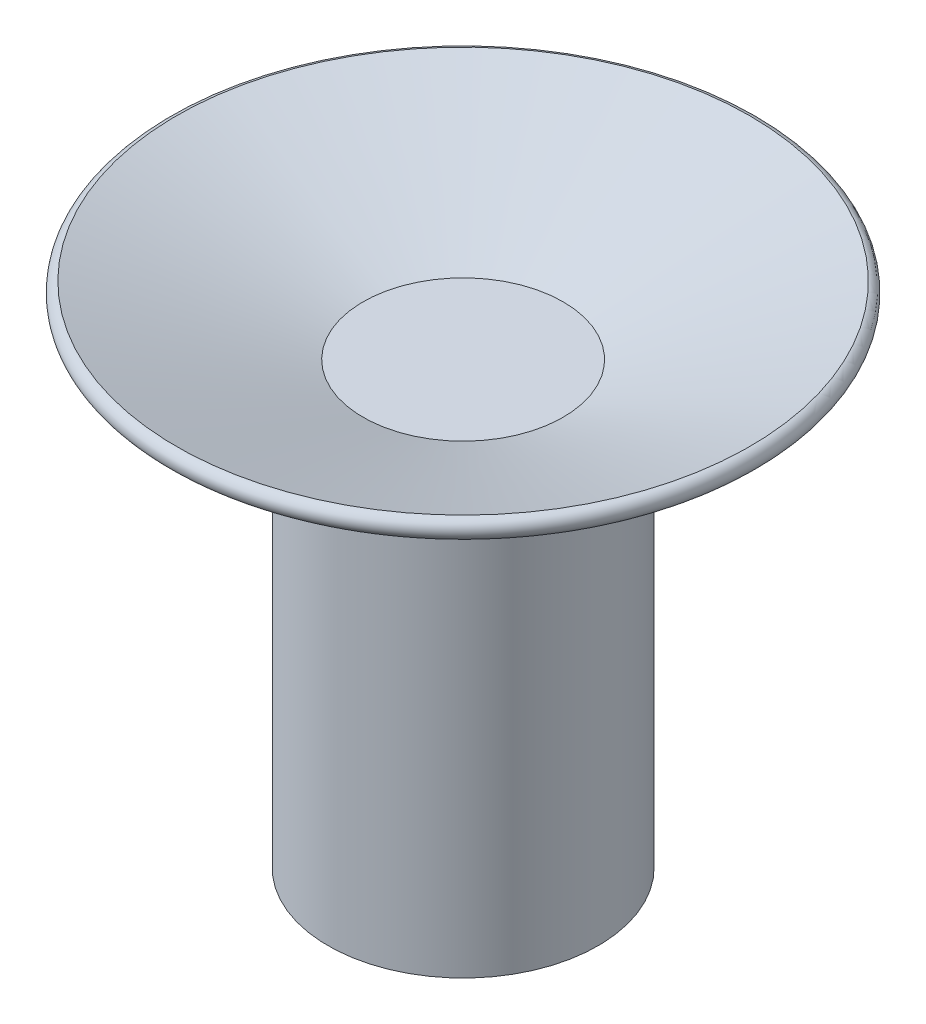
SolidWorks part; units mm, degrees
ref_plane "Plan de face" through (0, 0, 0) normal (0, 0, 1) x (1, 0, 0)
ref_plane "Plan de dessus" through (0, 0, 0) normal (0, 1, 0) x (1, 0, 0)
ref_plane "Plan de droite" through (0, 0, 0) normal (1, 0, 0) x (0, 0, -1)
sketch "Esquisse1" plane through (0, 0, 0) normal (0, 0, 1) x (1, 0, 0)
  line L0 (0, 0) -> (0, 11.1884) construction
  line L1 (0, 0) -> (5, 0)
  line L2 (5, 0) -> (14.3969, 3.4202)
  line L3 (0, 0) -> (0, 1)
  line L4 (14.3226, 4.3931) -> (5, 1)
  line L5 (5, 1) -> (0, 1)
  arc A0 (14.3969, 3.4202) -> (14.3226, 4.3931) centre (14.2237, 3.8963) ccw
  dimension "D1" = 5
  dimension "D2" = 160
  dimension "D3" = 1
  dimension "D4" = 10
revolve "Révolution1" add sketch "Esquisse1" angle 360 about L0
sketch "Esquisse2" plane through (0, 0, 0) normal (0, -1, 0) x (1, 0, 0)
  line L1 (2.7924, -4.1476) -> (4.9881, 0.3445)
  line L2 (4.9881, 0.3445) -> (2.1957, 4.4921)
  line L3 (2.1957, 4.4921) -> (-2.7924, 4.1476)
  line L4 (-2.7924, 4.1476) -> (-4.9881, -0.3445)
  line L5 (-4.9881, -0.3445) -> (-2.1957, -4.4921)
  line L6 (-2.1957, -4.4921) -> (2.7924, -4.1476)
  circle A0 centre (0, 0) radius 4.3301 construction
extrude "Boss.-Extru.1" add sketch "Esquisse2" along normal blind 1
sketch "Sketch1" plane through (0, -1, 0) normal (0, -1, 0) x (1, 0, 0)
  circle A0 centre (0, 0) radius 6.75
  dimension "D1" = 13.5
extrude "Boss-Extrude1" add sketch "Sketch1" along normal blind 20
